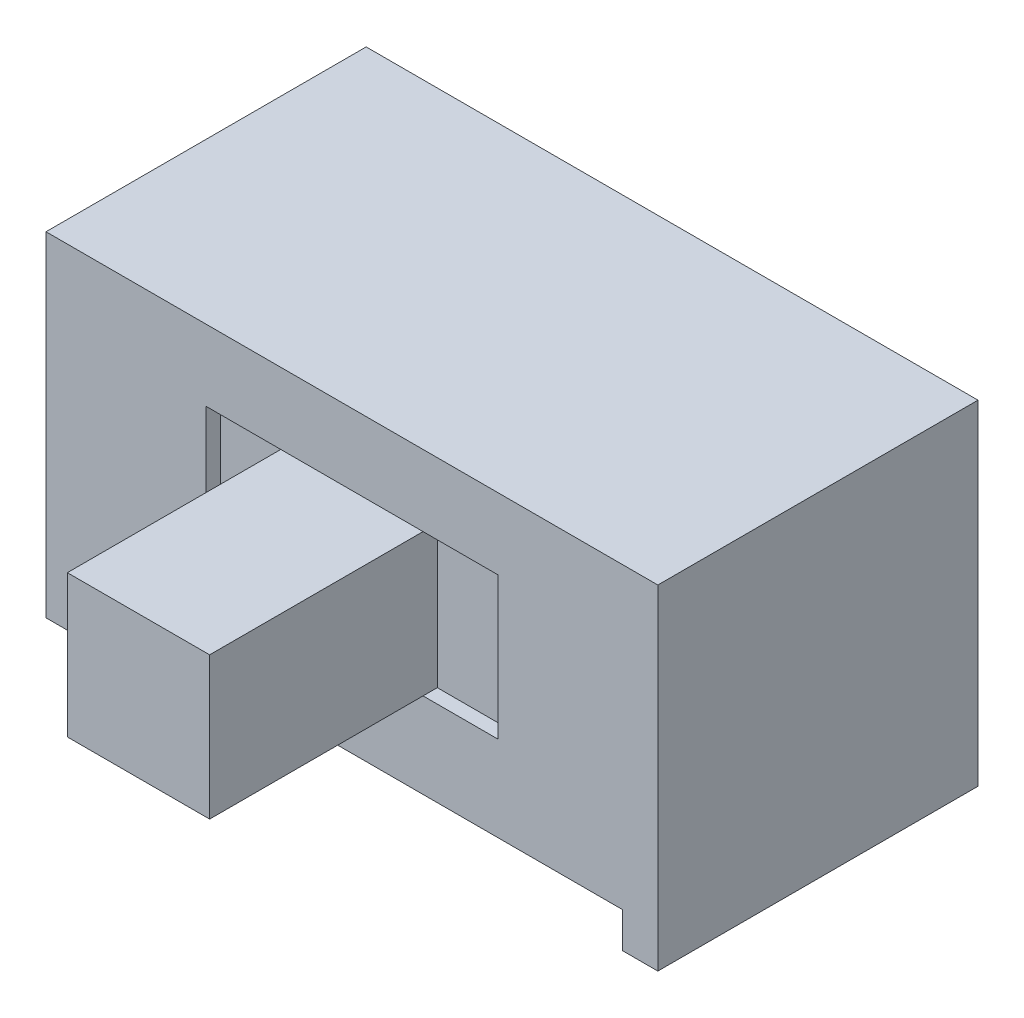
SolidWorks part; units mm, degrees
ref_plane "前视基准面" through (0, 0, 0) normal (0, 0, 1) x (1, 0, 0)
ref_plane "上视基准面" through (0, 0, 0) normal (0, 1, 0) x (1, 0, 0)
ref_plane "右视基准面" through (0, 0, 0) normal (1, 0, 0) x (0, 0, -1)
sketch "草图1" plane through (0, 0, 0) normal (0, 1, 0) x (1, 0, 0)
  line L1 (0, 0) -> (8.6, 0)
  line L2 (0, 0) -> (0, 4.5)
  line L3 (0, 4.5) -> (8.6, 4.5)
  line L4 (8.6, 0) -> (8.6, 4.5)
  dimension "D1" = 8.6
  dimension "D2" = 4.5
extrude "凸台-拉伸1" add sketch "草图1" along normal blind 4.7
sketch "草图2" plane through (0, 0, 0) normal (0, 0, 1) x (1, 0, 0)
  line L0 (4.3, 6.201) -> (4.3, -2.4586) construction
  line L1 (2.25, 3.7) -> (6.35, 3.7)
  line L2 (2.25, 3.7) -> (2.25, 1.7)
  line L3 (2.25, 1.7) -> (6.35, 1.7)
  line L4 (6.35, 3.7) -> (6.35, 1.7)
  line L7 (1.0818, 2.7) -> (7.44, 2.7) construction
  line L9 (0, 0) -> (8.6, 0) construction
  dimension "D1" = 4.1
  dimension "D2" = 2.7
  dimension "D3" = 2
extrude "切除-拉伸1" cut sketch "草图2" against normal blind 0.2
sketch "草图4" plane through (0, 0, 0) normal (0, 0, 1) x (1, 0, 0)
  line L0 (0.5, 0) -> (0.5, 0.5)
  line L1 (0, 0) -> (8.6, 0) construction
  line L2 (0.5, 0.5) -> (8.1, 0.5)
  line L3 (8.1, 0.5) -> (8.1, 0)
  line L4 (8.1, 0) -> (0.5, 0)
  line L6 (8.1, 0) -> (8.6, 0) construction
  line L7 (0.5, 0) -> (0, 0) construction
  dimension "D1" = 0.5
  dimension "D2" = 0.5
extrude "切除-拉伸2" cut sketch "草图4" against normal up to next
sketch "草图5" plane through (0, 0, 0) normal (0, 0, 1) x (1, 0, 0)
  line L0 (6.35, 3.7) -> (2.25, 3.7) construction
  line L1 (4.3, 4.5445) -> (4.3, -0.2014) construction
  line L2 (3.3, 3.7) -> (5.3, 3.7)
  line L3 (3.3, 3.7) -> (3.3, 1.7)
  line L4 (3.3, 1.7) -> (5.3, 1.7)
  line L5 (5.3, 3.7) -> (5.3, 1.7)
  line L6 (2.25, 1.7) -> (6.35, 1.7) construction
  point P12 (0, 0)
  dimension "D1" = 2
extrude "凸台-拉伸2" add sketch "草图5" along normal blind 3 and the other way up to surface (0.2 mm away) other way up to face at (4.3, 2.7, -0.2)
